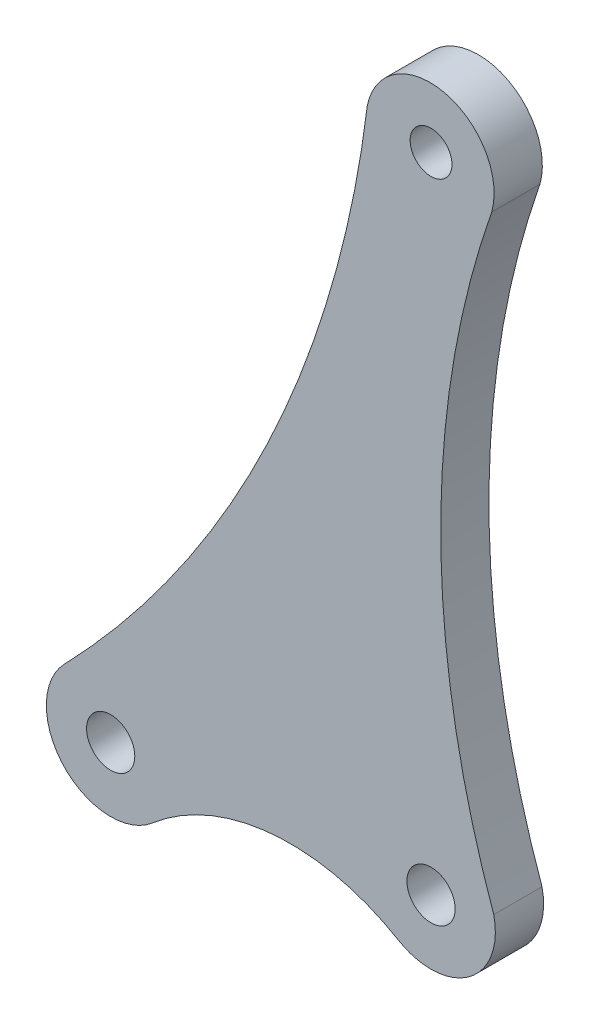
SolidWorks part; units mm, degrees
ref_plane "Front Plane" through (0, 0, 0) normal (0, 0, 1) x (1, 0, 0)
ref_plane "Top Plane" through (0, 0, 0) normal (0, 1, 0) x (1, 0, 0)
ref_plane "Right Plane" through (0, 0, 0) normal (1, 0, 0) x (0, 0, -1)
sketch "Model" plane through (0, 0, 0) normal (0, 0, 1) x (1, 0, 0)
  circle A0 centre (36.9616, 50.6677) radius 1.3
  circle A1 centre (17.0375, 8.9247) radius 1.5
  circle A2 centre (36.9615, 10.6676) radius 1.5
  arc A3 (14.1612, 11.7043) -> (19.644, 5.8904) centre (17.0381, 8.9251) ccw
  arc A4 (34.9214, 7.2271) -> (19.644, 5.8904) centre (28.214, -4.0854) ccw
  arc A5 (14.1612, 11.7043) -> (32.9916, 51.1563) centre (-35.3816, 59.5708) ccw
  arc A6 (40.7337, 49.3367) -> (40.8619, 11.5654) centre (94.324, 30.6328) ccw
  arc A7 (34.9214, 7.2271) -> (36.4627, 6.6989) centre (36.9614, 10.6678) ccw
  arc A8 (36.4627, 6.6989) -> (40.8619, 11.5654) centre (36.9562, 10.6745) ccw
  arc A9 (40.7337, 49.3367) -> (32.9916, 51.1563) centre (36.904, 50.4225) ccw
extrude "Boss-Extrude1" add sketch "Model" along normal blind 3
